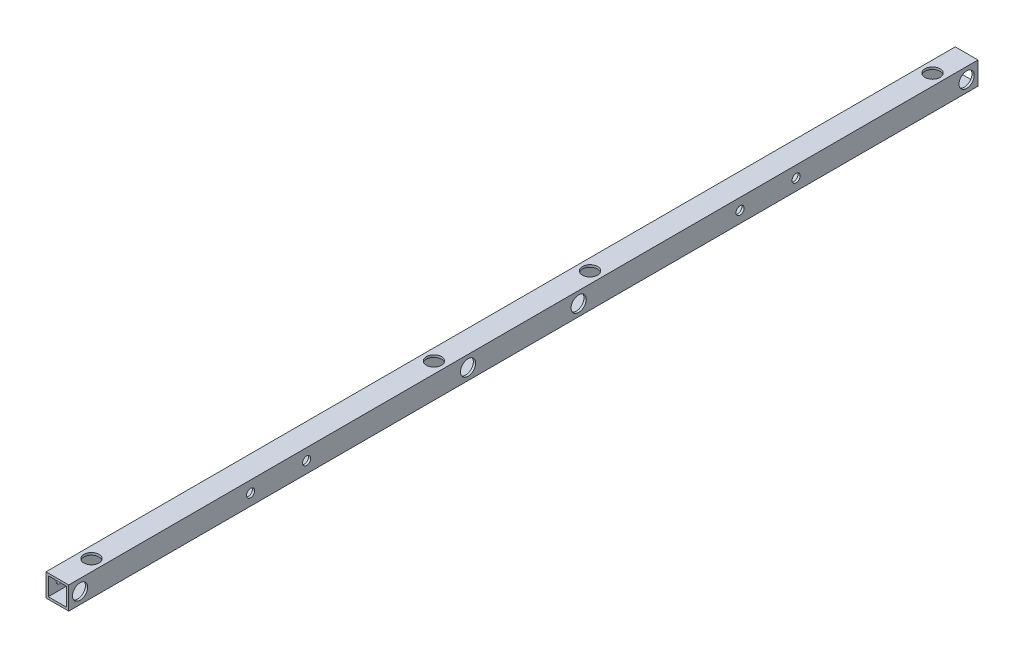
SolidWorks part; units mm, degrees
material "6063-T5"
ref_plane "正面" through (0, 0, 0) normal (0, 0, 1) x (1, 0, 0)
ref_plane "平面" through (0, 0, 0) normal (0, 1, 0) x (1, 0, 0)
ref_plane "右側面" through (0, 0, 0) normal (1, 0, 0) x (0, 0, -1)
sketch "ｽｹｯﾁ1" plane through (0, 0, 0) normal (0, 0, 1) x (1, 0, 0)
  line L1 (-7.5, -7.5) -> (7.5, -7.5)
  line L2 (-7.5, -7.5) -> (-7.5, 7.5)
  line L3 (-7.5, 7.5) -> (7.5, 7.5)
  line L4 (7.5, -7.5) -> (7.5, 7.5)
  line L5 (-7.5, -7.5) -> (7.5, 7.5) construction
  line L6 (-7.5, 7.5) -> (7.5, -7.5) construction
  line L7 (-6, -6) -> (6, -6)
  line L8 (-6, -6) -> (-6, 6)
  line L9 (-6, 6) -> (6, 6)
  line L10 (6, -6) -> (6, 6)
  line L11 (-6, -6) -> (6, 6) construction
  line L12 (-6, 6) -> (6, -6) construction
  point P0 (0, 0)
  point P6 (0, 0)
  dimension "D1" = 1.5
  dimension "D2" = 15
  dimension "D3" = 15
extrude "ﾎﾞｽ - 押し出し1" add sketch "ｽｹｯﾁ1" along normal blind 600
sketch "ｽｹｯﾁ2" plane through (7.5, 0, 0) normal (1, 0, 0) x (0, 0, -1)
  line L0 (-600, -7.5) -> (0, -7.5) construction
  line L1 (0, -7.5) -> (0, 7.5) construction
  line L2 (-600, -7.5) -> (-600, 7.5) construction
  line L3 (-600, 7.5) -> (0, 7.5) construction
  circle A4 centre (-592.5, 0) radius 2.25
  circle A8 centre (-7.5, 0) radius 2.25
  circle A9 centre (-336.5, 0) radius 2.25
  circle A10 centre (-263.5, 0) radius 2.25
  point P12 (-300, 7.5)
  dimension "D1" = 4.5
  dimension "D2" = 7.5
  dimension "D3" = 7.5
  dimension "D6" = 36.5
  dimension "D7" = 2
  dimension "D8" = 73
  dimension "D4" = 7.5
  dimension "D9" = 2
  dimension "D5" = 2
extrude "ｶｯﾄ - 押し出し1" cut sketch "ｽｹｯﾁ2" against normal blind 25
sketch "ｽｹｯﾁ3" plane through (0, 7.5, 0) normal (0, 1, 0) x (1, 0, 0)
  line L0 (-7.5, -600) -> (-7.5, 0) construction
  line L2 (7.5, -600) -> (7.5, 0) construction
  line L3 (7.5, 0) -> (-7.5, 0) construction
  circle A1 centre (0, -22.5) radius 2.25
  circle A6 centre (0, -577.5) radius 2.25
  circle A7 centre (0, -351.5) radius 2.25
  circle A8 centre (0, -248.5) radius 2.25
  point P12 (-7.5, -300)
  dimension "D2" = 22.5
  dimension "D3" = 4.5
  dimension "D7" = 103
  dimension "D8" = 2
  dimension "D9" = 7.5
  dimension "D11" = 22.5
  dimension "D4" = 7.5
  dimension "D5" = 4.5
  dimension "D10" = 51.5
  dimension "D6" = 2
extrude "ｶｯﾄ - 押し出し2" cut sketch "ｽｹｯﾁ3" against normal blind 25
sketch "ｽｹｯﾁ4" plane through (0, 7.5, 0) normal (0, 1, 0) x (1, 0, 0)
  circle A0 centre (0, -577.5) radius 5
  circle A1 centre (0, -351.5) radius 5
  circle A2 centre (0, -248.5) radius 5
  circle A3 centre (0, -22.5) radius 5
  dimension "D1" = 10
  dimension "D2" = 10
  dimension "D3" = 10
  dimension "D4" = 10
extrude "ｶｯﾄ - 押し出し3" cut sketch "ｽｹｯﾁ4" against normal blind 10
sketch "ｽｹｯﾁ5" plane through (7.5, 0, 0) normal (1, 0, 0) x (0, 0, -1)
  circle A0 centre (-592.5, 0) radius 5
  circle A1 centre (-336.5, 0) radius 5
  circle A2 centre (-263.5, 0) radius 5
  circle A3 centre (-7.5, 0) radius 5
  dimension "D1" = 10
  dimension "D2" = 10
  dimension "D3" = 10
  dimension "D4" = 10
extrude "ｶｯﾄ - 押し出し4" cut sketch "ｽｹｯﾁ5" against normal blind 10
sketch "ｽｹｯﾁ6" plane through (7.5, 0, 0) normal (1, 0, 0) x (0, 0, -1)
  line L0 (-600, -7.5) -> (-600, 7.5) construction
  line L1 (-600, -7.5) -> (0, -7.5) construction
  line L2 (0, -7.5) -> (0, 7.5) construction
  circle A0 centre (-480, 0) radius 2.7
  circle A1 centre (-443, 0) radius 2.7
  circle A2 centre (-157, 0) radius 2.7
  circle A3 centre (-120, 0) radius 2.7
  dimension "D1" = 5.4
  dimension "D3" = 37
  dimension "D4" = 7.5
  dimension "D5" = 7.5
  dimension "D6" = 5.4
  dimension "D8" = 120
  dimension "D2" = 120
  dimension "D7" = 2
extrude "ｶｯﾄ - 押し出し5" cut sketch "ｽｹｯﾁ6" against normal blind 20
sketch "ｽｹｯﾁ7" plane through (-7.5, 0, 0) normal (-1, 0, 0) x (0, 0, 1)
  circle A0 centre (120, 0) radius 5
  circle A1 centre (157, 0) radius 5
  circle A2 centre (443, 0) radius 5
  circle A3 centre (480, 0) radius 5
  dimension "D1" = 10
  dimension "D2" = 10
  dimension "D3" = 10
  dimension "D4" = 10
extrude "ｶｯﾄ - 押し出し6" cut sketch "ｽｹｯﾁ7" against normal blind 3
